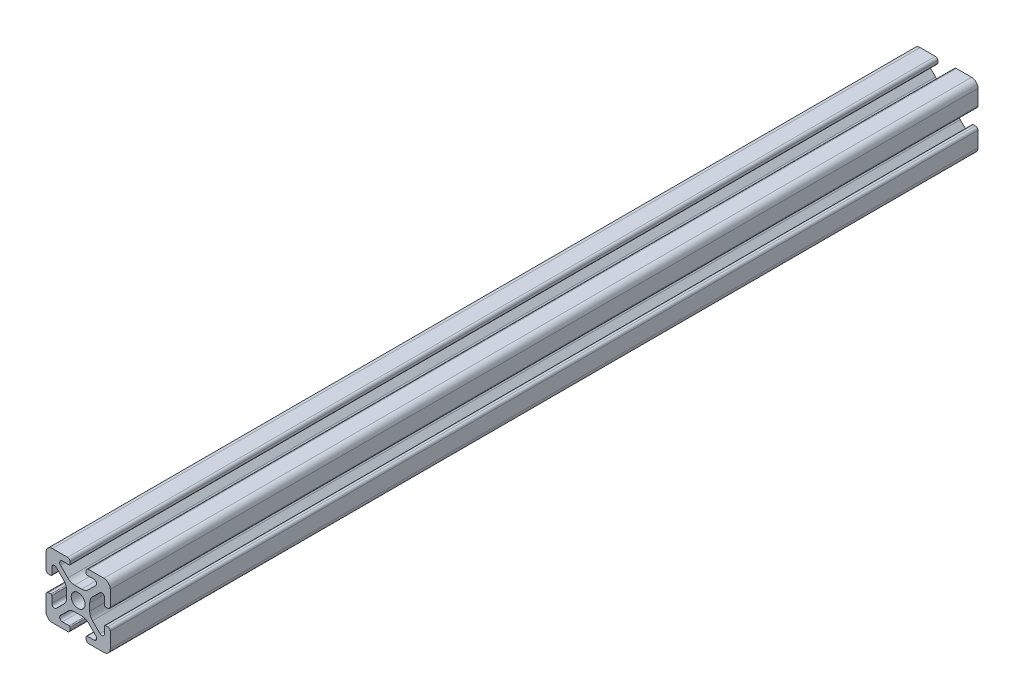
SolidWorks part; units mm, degrees
ref_plane "Front Plane" through (0, 0, 0) normal (0, 0, 1) x (1, 0, 0)
ref_plane "Top Plane" through (0, 0, 0) normal (0, 1, 0) x (1, 0, 0)
ref_plane "Right Plane" through (0, 0, 0) normal (1, 0, 0) x (0, 0, -1)
sketch "Sketch1" plane through (0, 0, 0) normal (0, 0, 1) x (1, 0, 0)
  line L0 (0, 10) -> (0, -10) construction
  line L1 (10, 0) -> (-10, 0) construction
  line L2 (-2.5, 10) -> (2.5, 10) construction
  line L3 (-5.75, 8.2) -> (5.75, 8.2) construction
  circle A0 centre (0, 0) radius 2.15 construction
  point P4 (0, 0)
  point P8 (0, 0)
  point P10 (0, 3.6)
  point P14 (0, 10)
  point P17 (0, 8.2)
  dimension "Thru Hole" = 4.3
  dimension "Height" = 20
  dimension "T Slot Depth" = 6.4
  dimension "T Slot Top Width" = 5
  dimension "T Slot Max Width" = 11.5
  dimension "Wall" = 1.8
sketch "Sketch2" plane through (0, 0, 0) normal (1, 0, 0) x (0, 0, -1)
  line L0 (135, 0) -> (-135, 0) construction
  point P4 (0, 0)
  dimension "D1" = 270
sketch "Sketch3" plane through (0, 0, 0) normal (0, 0, 1) x (1, 0, 0)
  line L0 (3.2874, 10) -> (8, 10)
  line L1 (10, 8) -> (10, -8) construction
  line L2 (8, -10) -> (-8, -10) construction
  line L3 (-10, 10) -> (10, -10) construction
  line L4 (2.5, 9.2126) -> (2.5, 8.5048)
  line L5 (-5.75, 8.2) -> (5.75, 8.2) construction
  line L6 (2.8048, 8.2) -> (4.9118, 8.2)
  line L7 (5.5045, 6.7691) -> (3.2141, 4.4787)
  line L8 (1.0928, 3.6) -> (-1.0928, 3.6)
  line L9 (0, 10) -> (0, -10) construction
  line L10 (5.75, 8.2) -> (5.75, 0) construction
  line L11 (10, 0) -> (-10, 0) construction
  line L12 (0, 0) -> (0, 10) construction
  line L13 (-2.5, 9.2126) -> (-2.5, 8.5048)
  line L14 (-5.5045, 6.7691) -> (-3.2141, 4.4787)
  line L15 (-2.8048, 8.2) -> (-4.9118, 8.2)
  line L16 (-3.2874, 10) -> (-8, 10)
  line L17 (0, 0) -> (-10, 0) construction
  line L18 (-10, 3.2874) -> (-10, 8)
  line L19 (-8.2, 2.8048) -> (-8.2, 4.9118)
  line L20 (-6.7691, 5.5045) -> (-4.4787, 3.2141)
  line L21 (-9.2126, 2.5) -> (-8.5048, 2.5)
  line L22 (-3.6, -1.0928) -> (-3.6, 1.0928)
  line L23 (-6.7691, -5.5045) -> (-4.4787, -3.2141)
  line L24 (-8.2, -2.8048) -> (-8.2, -4.9118)
  line L25 (-9.2126, -2.5) -> (-8.5048, -2.5)
  line L26 (-10, -3.2874) -> (-10, -8)
  line L27 (9.2126, -2.5) -> (8.5048, -2.5)
  line L28 (8.2, -2.8048) -> (8.2, -4.9118)
  line L29 (6.7691, -5.5045) -> (4.4787, -3.2141)
  line L30 (3.6, -1.0928) -> (3.6, 1.0928)
  line L31 (9.2126, 2.5) -> (8.5048, 2.5)
  line L32 (6.7691, 5.5045) -> (4.4787, 3.2141)
  line L33 (8.2, 2.8048) -> (8.2, 4.9118)
  line L34 (10, 8) -> (10, 3.2874)
  line L35 (10, -3.2874) -> (10, -8)
  line L36 (3.2874, -10) -> (8, -10)
  line L37 (-3.2874, -10) -> (-8, -10)
  line L38 (-6.7691, -5.5045) -> (-4.4787, -3.2141)
  line L39 (-2.8048, -8.2) -> (-4.9118, -8.2)
  line L40 (-5.5045, -6.7691) -> (-3.2141, -4.4787)
  line L41 (-2.5, -9.2126) -> (-2.5, -8.5048)
  line L42 (1.0928, -3.6) -> (-1.0928, -3.6)
  line L43 (5.5045, -6.7691) -> (3.2141, -4.4787)
  line L44 (2.8048, -8.2) -> (4.9118, -8.2)
  line L45 (2.5, -9.2126) -> (2.5, -8.5048)
  arc A0 (4.9118, 8.2) -> (5.5045, 6.7691) centre (4.9118, 7.3618) cw
  arc A1 (3.2141, 4.4787) -> (1.0928, 3.6) centre (1.0928, 6.6) cw
  circle A2 centre (0, 0) radius 2.15 construction
  circle A3 centre (0, 0) radius 2.15
  arc A4 (3.2874, 10) -> (2.5, 9.2126) centre (3.2874, 9.2126) ccw
  arc A5 (2.5, 8.5048) -> (2.8048, 8.2) centre (2.8048, 8.5048) ccw
  arc A6 (-3.2874, 10) -> (-2.5, 9.2126) centre (-3.2874, 9.2126) cw
  arc A7 (-4.9118, 8.2) -> (-5.5045, 6.7691) centre (-4.9118, 7.3618) ccw
  arc A8 (-3.2141, 4.4787) -> (-1.0928, 3.6) centre (-1.0928, 6.6) ccw
  arc A9 (-2.5, 8.5048) -> (-2.8048, 8.2) centre (-2.8048, 8.5048) cw
  arc A10 (-8.5048, 2.5) -> (-8.2, 2.8048) centre (-8.5048, 2.8048) ccw
  arc A11 (-4.4787, 3.2141) -> (-3.6, 1.0928) centre (-6.6, 1.0928) cw
  arc A12 (-8.2, 4.9118) -> (-6.7691, 5.5045) centre (-7.3618, 4.9118) cw
  arc A13 (-10, 3.2874) -> (-9.2126, 2.5) centre (-9.2126, 3.2874) ccw
  arc A14 (-8.5048, -2.5) -> (-8.2, -2.8048) centre (-8.5048, -2.8048) cw
  arc A15 (-10, -3.2874) -> (-9.2126, -2.5) centre (-9.2126, -3.2874) cw
  arc A16 (-4.4787, -3.2141) -> (-3.6, -1.0928) centre (-6.6, -1.0928) ccw
  arc A17 (-8.2, -4.9118) -> (-6.7691, -5.5045) centre (-7.3618, -4.9118) ccw
  arc A26 (-8, -10) -> (-10, -8) centre (-8, -8) cw
  arc A27 (-8, 10) -> (-10, 8) centre (-8, 8) ccw
  arc A28 (8, 10) -> (10, 8) centre (8, 8) cw
  arc A29 (10, -8) -> (8, -10) centre (8, -8) cw
  arc A30 (8.2, -4.9118) -> (6.7691, -5.5045) centre (7.3618, -4.9118) cw
  arc A31 (4.4787, -3.2141) -> (3.6, -1.0928) centre (6.6, -1.0928) cw
  arc A32 (10, -3.2874) -> (9.2126, -2.5) centre (9.2126, -3.2874) ccw
  arc A33 (8.5048, -2.5) -> (8.2, -2.8048) centre (8.5048, -2.8048) ccw
  arc A34 (10, 3.2874) -> (9.2126, 2.5) centre (9.2126, 3.2874) cw
  arc A35 (8.2, 4.9118) -> (6.7691, 5.5045) centre (7.3618, 4.9118) ccw
  arc A36 (4.4787, 3.2141) -> (3.6, 1.0928) centre (6.6, 1.0928) ccw
  arc A37 (8.5048, 2.5) -> (8.2, 2.8048) centre (8.5048, 2.8048) cw
  arc A38 (-2.5, -8.5048) -> (-2.8048, -8.2) centre (-2.8048, -8.5048) ccw
  arc A39 (-3.2141, -4.4787) -> (-1.0928, -3.6) centre (-1.0928, -6.6) cw
  arc A40 (-4.9118, -8.2) -> (-5.5045, -6.7691) centre (-4.9118, -7.3618) cw
  arc A41 (-3.2874, -10) -> (-2.5, -9.2126) centre (-3.2874, -9.2126) ccw
  arc A42 (2.5, -8.5048) -> (2.8048, -8.2) centre (2.8048, -8.5048) cw
  arc A43 (3.2874, -10) -> (2.5, -9.2126) centre (3.2874, -9.2126) cw
  arc A44 (3.2141, -4.4787) -> (1.0928, -3.6) centre (1.0928, -6.6) ccw
  arc A45 (4.9118, -8.2) -> (5.5045, -6.7691) centre (4.9118, -7.3618) ccw
  point P36 (2.5, 10)
  point P39 (2.5, 8.2)
  point P49 (0, 3.6)
  point P77 (-3.6, 0)
  point P78 (-8.2, -2.5)
  point P79 (-10, -2.5)
  point P104 (-10, -10)
  point P110 (10, 10)
  point P114 (10, -2.5)
  point P115 (8.2, -2.5)
  point P116 (3.6, 0)
  point P141 (0, -3.6)
  dimension "D1" = 3
  dimension "D2" = 0.8382
  dimension "D4" = 0.7874
  dimension "D5" = 0.3048
  dimension "D6" = 2
  dimension "D3" = 45
extrude "Boss-Extrude1" add sketch "Sketch3" along normal up to vertex (135 mm away) and the other way up to vertex (135 mm away) contours A45 L44 A42 L45 A43 L36 A29 L35 A32 L27 A33 L28 A30 L29 A31 L30 A36 L32 A35 L33 A37 L31 A34 L34 A28 L0 A4 L4 A5 L6 A0 L7 A1 L8 A8 L14 A7 L15 A9 L13 A6 L16 A27 L18 A13 L21 A10 L19 A12 L20 A11 up to point (0, 0, 135) other way up to point (0, 0, -135)
